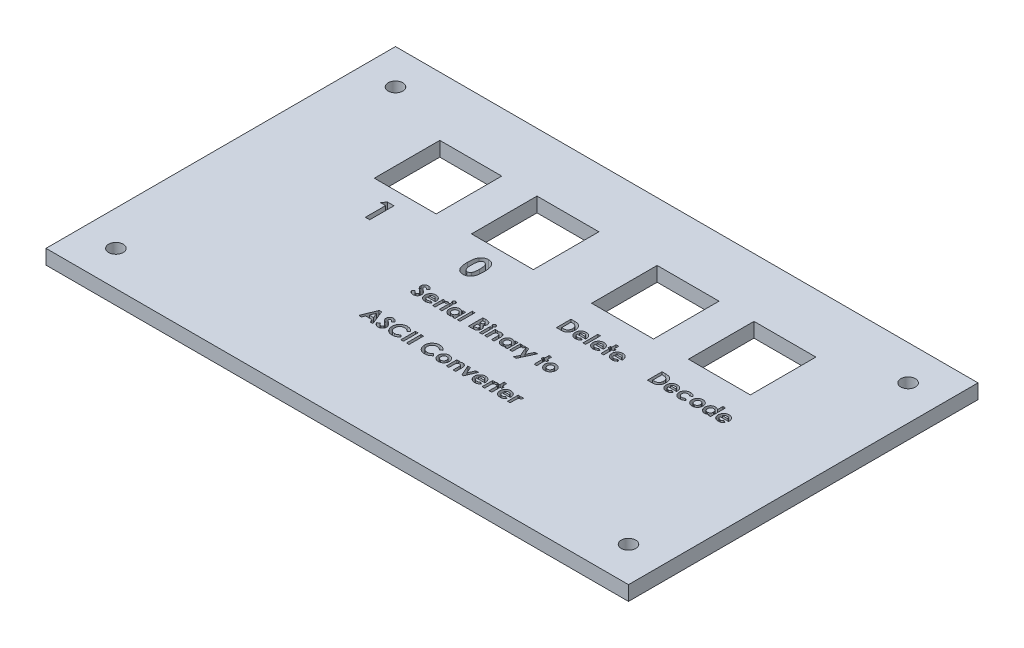
SolidWorks part; units mm, degrees
ref_plane "Front Plane" through (0, 0, 0) normal (0, 0, 1) x (1, 0, 0)
ref_plane "Top Plane" through (0, 0, 0) normal (0, 1, 0) x (1, 0, 0)
ref_plane "Right Plane" through (0, 0, 0) normal (1, 0, 0) x (0, 0, -1)
sketch "Sketch1" plane through (0, 0, 0) normal (0, 1, 0) x (1, 0, 0)
  line L1 (-63.5, 38.1) -> (63.5, 38.1)
  line L2 (-63.5, 38.1) -> (-63.5, -38.1)
  line L3 (-63.5, -38.1) -> (63.5, -38.1)
  line L4 (63.5, 38.1) -> (63.5, -38.1)
  point P4 (0, 38.1)
  point P6 (-63.5, 0)
  dimension "D1" = 127
  dimension "D2" = 76.2
extrude "Boss-Extrude1" add sketch "Sketch1" along normal blind 3.175
sketch "Sketch2" plane through (0, 0, 0) normal (0, 1, 0) x (1, 0, 0)
  line L0 (-63.5, 38.1) -> (-63.5, -38.1) construction
  line L1 (63.5, 38.1) -> (-63.5, 38.1) construction
  line L2 (-63.5, -38.1) -> (63.5, -38.1) construction
  line L3 (63.5, -38.1) -> (63.5, 38.1) construction
  line L4 (-40.9575, 16.8073) -> (-63.5, 16.8073) construction
  line L5 (-27.4637, 10.9309) -> (-40.9575, 10.9309)
  line L6 (-27.4637, 10.9309) -> (-27.4637, 25.2184)
  line L7 (-27.4637, 25.2184) -> (-40.9575, 25.2184)
  line L8 (-40.9575, 10.9309) -> (-40.9575, 25.2184)
  line L9 (-27.4637, 10.9309) -> (-40.9575, 25.2184) construction
  line L10 (-27.4637, 25.2184) -> (-40.9575, 10.9309) construction
  line L11 (-19.8437, 25.2948) -> (-6.35, 25.2948)
  line L12 (-19.8437, 25.2948) -> (-19.8437, 11.0073)
  line L13 (-19.8437, 11.0073) -> (-6.35, 11.0073)
  line L14 (-6.35, 25.2948) -> (-6.35, 11.0073)
  line L15 (6.35, 25.2948) -> (19.8437, 25.2948)
  line L16 (6.35, 25.2948) -> (6.35, 11.0073)
  line L17 (6.35, 11.0073) -> (19.8437, 11.0073)
  line L18 (19.8437, 25.2948) -> (19.8437, 11.0073)
  line L19 (27.4637, 25.2948) -> (40.9575, 25.2948)
  line L20 (27.4637, 25.2948) -> (27.4637, 11.0073)
  line L21 (27.4637, 11.0073) -> (40.9575, 11.0073)
  line L22 (40.9575, 25.2948) -> (40.9575, 11.0073)
  line L23 (40.9575, 15.4077) -> (63.5, 15.4077) construction
  circle A0 centre (-55.88, 30.48) radius 1.5875
  circle A1 centre (-55.88, -30.48) radius 1.5875
  circle A2 centre (55.88, 30.48) radius 1.5875
  circle A3 centre (55.88, -30.48) radius 1.5875
  point P16 (-34.2106, 18.0747)
  dimension "D1" = 7.62
  dimension "D3" = 7.62
  dimension "D5" = 7.62
  dimension "D2" = 7.62
  dimension "D4" = 7.62
  dimension "D7" = 14.2875
  dimension "D9" = 7.62
  dimension "D11" = 12.7
  dimension "D13" = 7.62
extrude "Cut-Extrude3" cut sketch "Sketch2" along normal through all
sketch "Sketch3" plane through (0, 3.175, 0) normal (0, 1, 0) x (1, 0, 0)
  line L0 (-39.0243, 2.5782) -> (-29.3969, 2.5782) construction
  line L1 (-16.9979, 2.5782) -> (-9.1958, 2.5782) construction
  line L2 (6.7469, 2.5782) -> (19.4469, 2.5782) construction
  line L3 (26.5906, 2.5782) -> (41.8306, 2.5782) construction
  line L4 (-40.9575, 10.9309) -> (-27.4637, 10.9309) construction
  line L5 (-19.8437, 11.0073) -> (-6.35, 11.0073) construction
  line L6 (6.35, 11.0073) -> (19.8437, 11.0073) construction
  line L7 (27.4637, 11.0073) -> (40.9575, 11.0073) construction
  line L8 (-24.3685, -6.7574) -> (24.6439, -6.7574) construction
  line L9 (-36.184, -16.6766) -> (36.4593, -16.6766) construction
  text T0 "<b>1</b>" font "Century Gothic" height in points 20
  text T1 "<b>0</b>" font "Century Gothic" height in points 20
  text T2 "<b>Delete</b>"
  text T3 "<b>Decode</b>"
  text T4 "<b>Serial Binary to </b>"
  text T5 "<b>ASCII Converter</b>"
  point P8 (-34.2106, 2.5782)
  point P11 (-34.2106, 10.9309)
  point P12 (-13.0969, 2.5782)
  point P15 (-13.0969, 11.0073)
  point P16 (13.0969, 2.5782)
  point P19 (13.0969, 11.0073)
  point P20 (34.2106, 2.5782)
  point P23 (34.2106, 11.0073)
  point P30 (0.1377, -6.7574)
  point P31 (0.1377, -16.6766)
extrude "Cut-Extrude4" cut sketch "Sketch3" against normal through all
